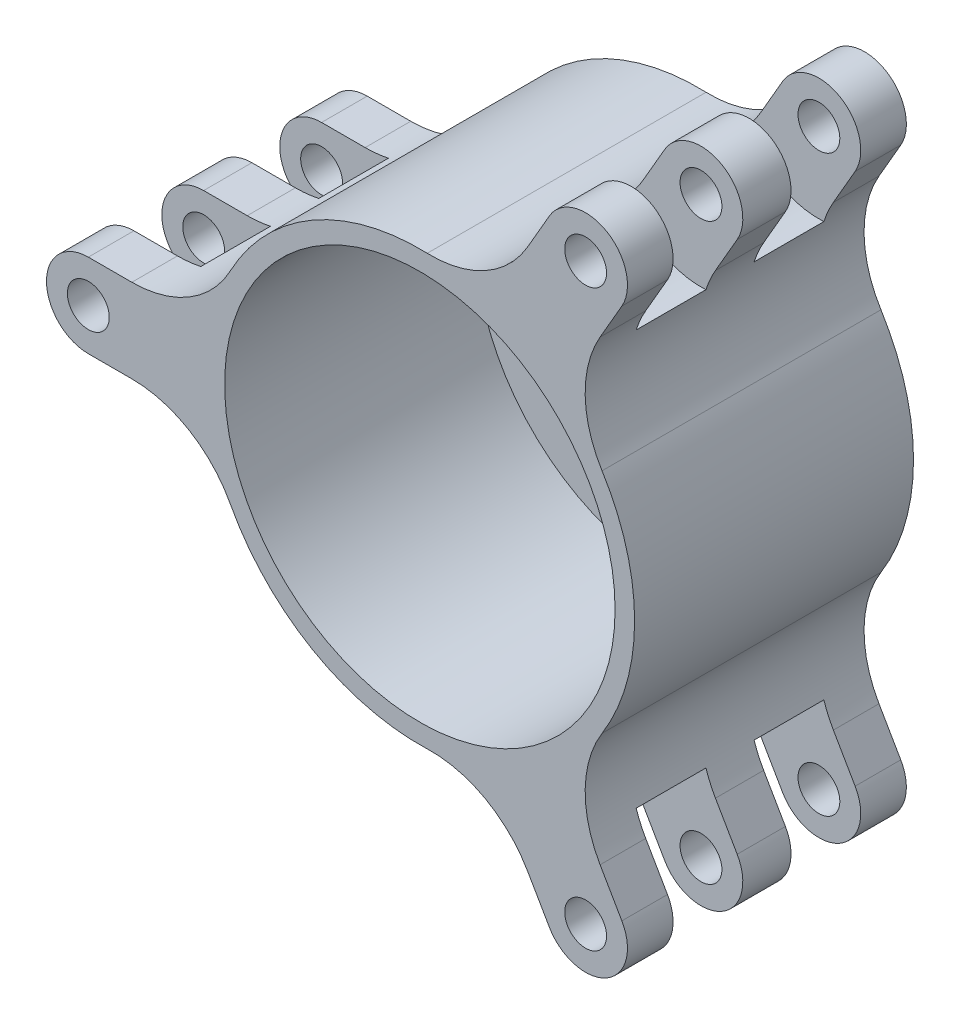
SolidWorks part; units mm, degrees
ref_plane "Front Plane" through (0, 0, 0) normal (0, 0, 1) x (1, 0, 0)
ref_plane "Top Plane" through (0, 0, 0) normal (0, 1, 0) x (1, 0, 0)
ref_plane "Right Plane" through (0, 0, 0) normal (1, 0, 0) x (0, 0, -1)
sketch "Sketch1" plane through (0, 0, 0) normal (0, 0, 1) x (1, 0, 0)
  line L0 (0, 0) -> (-35.6343, 0) construction
  line L1 (-14, 0) -> (-18.775, 0) construction
  line L2 (0, 0) -> (-24.6626, 42.7168) construction
  line L4 (11.8875, 20.5898) -> (-18.257, -31.6221) construction
  circle A0 centre (0, 0) radius 15.4
  circle A1 centre (-23.775, 0) radius 1.5 construction
  circle A2 centre (-23.775, 0) radius 5 construction
  circle A3 centre (11.8875, 20.5898) radius 5 construction
  circle A5 centre (11.8875, -20.5898) radius 5 construction
  circle A7 centre (0, 0) radius 14 construction
  circle A10 centre (0, 0) radius 28.775 construction
  circle A12 centre (-23.775, 0) radius 5.75 construction
  point P4 (-7.7, -13.3368)
  point P10 (7.8774, 23.5762)
  point P14 (-7.7, 13.3368)
  point P15 (15.4, 0)
  point P16 (32.5084, 33.0381)
  point P17 (-24.3563, 4.9661)
  point P18 (16.4789, 18.6102)
  point P24 (0, 0)
  point P25 (0, 0)
  point P26 (0, 0)
  point P28 (-77.5288, 5.4916)
  point P31 (-23.775, -5)
  point P32 (16.4789, -18.6102)
  point P34 (0, 0)
  point P35 (0, 0)
  point P36 (0, 0)
  point P37 (0, 0)
  point P39 (0, 0)
  point P40 (7.8774, -23.5762)
  dimension "D2" = 3
  dimension "D3" = 10
  dimension "D10" = 11.5
  dimension "D7" = 60
  dimension "D4" = 3
extrude "Boss-Extrude1" add sketch "Sketch1" along normal blind 20
sketch "Sketch6" plane through (0, 0, 20) normal (0, 0, 1) x (1, 0, 0)
  line L1 (-23.775, 3) -> (-15.105, 3)
  line L2 (-23.775, -3) -> (-15.105, -3)
  arc A0 (-23.775, 3) -> (-23.775, -3) centre (-23.775, 0) ccw
  circle A1 centre (0, 0) radius 15.4 construction
  arc A2 (-15.105, 3) -> (-15.105, -3) centre (0, 0) ccw
  dimension "D1" = 6
extrude "Boss-Extrude2" add sketch "Sketch6" against normal up to surface (20 mm away) up to face at (15.4, 0, 0)
fillet "Fillet4" radius 8 2 edges at (-15.105, -3, 10) (-15.105, 3, 10)
pattern_circular "CirPattern11" count 3 over 360 about axis through (0, 0, 0) along (0, 0, 1) of "Fillet4", "Boss-Extrude2"
sketch "Sketch4" plane through (0, 0, 20) normal (0, 0, 1) x (1, 0, 0)
  circle A0 centre (0, 0) radius 14 construction
  circle A1 centre (0, 0) radius 14
extrude "Cut-Extrude3" cut sketch "Sketch4" against normal offset from surface (18 mm away) 2
sketch "Sketch5" plane through (0, 0, 2) normal (0, 0, 1) x (1, 0, 0)
  circle A0 centre (0, 0) radius 5
  dimension "D1" = 10
extrude "Cut-Extrude4" cut sketch "Sketch5" against normal through all both and the other way through all
sketch "Sketch7" plane through (0, 0, 2) normal (0, 0, 1) x (1, 0, 0)
  line L0 (200000, 0) -> (-200035.6343, 0) construction
  line L1 (-5.4, 0) -> (-5, 0) construction
  circle A0 centre (-8.4, 0) radius 3
  circle A2 centre (0, 0) radius 5 construction
  dimension "D1" = 0.4
  dimension "D2" = 6
extrude "Cut-Extrude5" cut sketch "Sketch7" against normal through all both and the other way through all
pattern_circular "CirPattern12" count 4 over 360 about axis through (0, 0, 0) along (0, 0, 1) of "Cut-Extrude5"
sketch "Sketch2" plane through (0, 0, 20) normal (0, 0, 1) x (1, 0, 0)
  circle A2 centre (-23.775, 0) radius 1.5 construction
  circle A5 centre (-23.775, 0) radius 1.5
  point P10 (-0.25, -0.1443)
extrude "Cut-Extrude1" cut sketch "Sketch2" against normal through all both and the other way through all
pattern_circular "CirPattern10" count 3 over 360 about axis through (0, 0, 0) along (0, 0, 1) of "Cut-Extrude1"
ref_plane "roller plane" through (0, 0, 5.7716) normal (0, 0, 1) x (1, 0, 0)
sketch "Sketch3" plane through (0, 0, 5.7716) normal (0, 0, 1) x (1, 0, 0)
  circle A0 centre (-23.775, 0) radius 5.75 construction
  circle A1 centre (-23.775, 0) radius 5.75
extrude "Cut-Extrude2" cut sketch "Sketch3" against normal mid plane 5
pattern_circular "CirPattern3" count 3 over 360 about axis through (0, 0, 0) along (0, 0, 1) of "Cut-Extrude2"
ref_plane "mid plane" through (0, 0, 10) normal (0, 0, 1) x (1, 0, 0)
mirror "Mirror1" about plane through (0, 0, 10) normal (0, 0, 1) of "Cut-Extrude2", "CirPattern3"
equation "\"flex_pitch_dia\"= 56mm'flex spline pitch diameter"
equation "\"circ_pitch_dia\"= 62.05mm'circular spline pitch diameter (desired diameter after deformation)"
equation "\"clearence\"= 0.8mm"
equation "\"flex_inner_circ_to_pitch_dia\"= 1.45mm'distance between \"cup\" and pitch circle"
equation "\"wave_drive_dia\"= \"circ_pitch_dia\" - 2 * \"flex_inner_circ_to_pitch_dia\" - 2 * \"clearence\""
equation "\"D6@Sketch1\"= \"wave_drive_dia\""
equation "\"bearing_dia\"= 10mm"
equation "\"D3@Sketch1\"= \"bearing_dia\""
equation "\"D10@Sketch1\"= \"bearing_dia\" + 1.5"
equation "\"embedded_motor_dia\"= 28mm"
equation "\"D5@Sketch1\"= \"embedded_motor_dia\""
